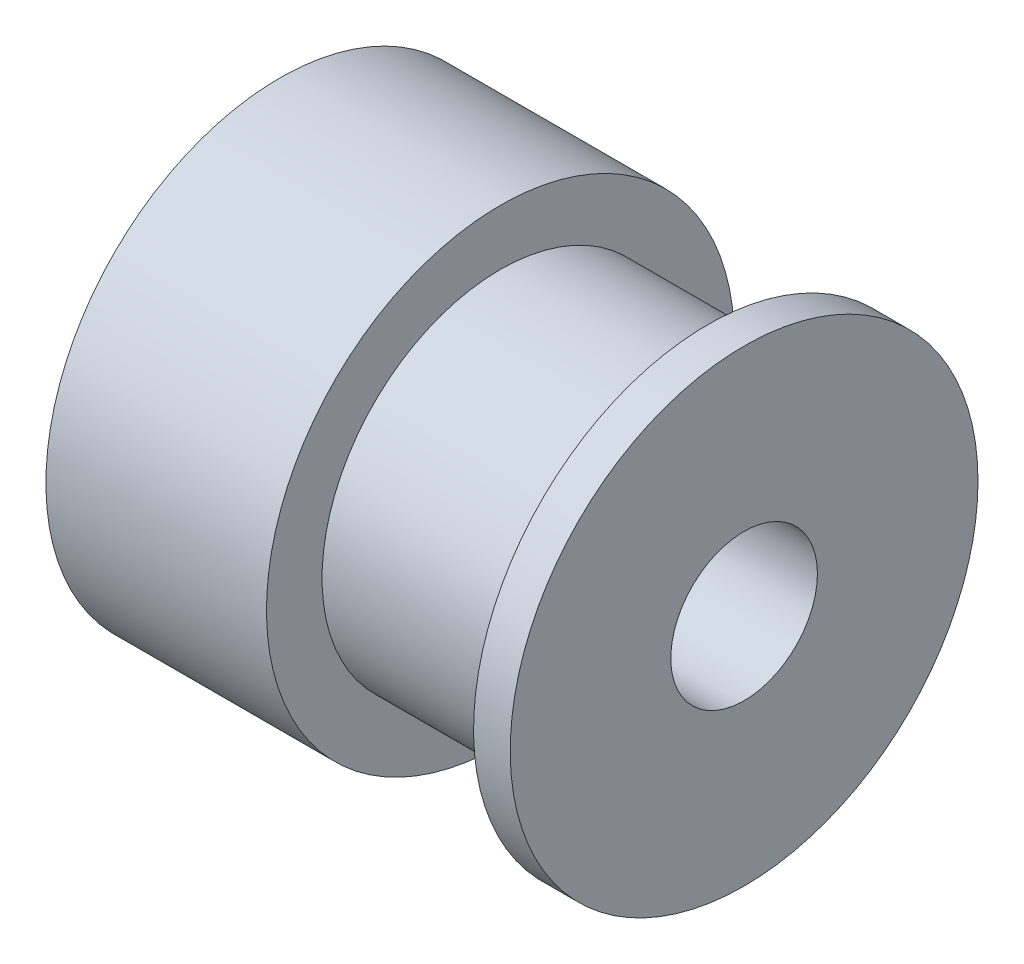
SolidWorks part; units mm, degrees
ref_plane "Front Plane" through (0, 0, 0) normal (0, 0, 1) x (1, 0, 0)
ref_plane "Top Plane" through (0, 0, 0) normal (0, 1, 0) x (1, 0, 0)
ref_plane "Right Plane" through (0, 0, 0) normal (1, 0, 0) x (0, 0, -1)
sketch "Sketch1" plane through (0, 0, 0) normal (1, 0, 0) x (0, 0, -1)
  circle A0 centre (0, 0) radius 7.975
  dimension "D1" = 15.95
extrude "Boss-Extrude1" add sketch "Sketch1" along normal blind 15.83
sketch "Sketch2" plane through (0, 0, 0) normal (0, 0, 1) x (1, 0, 0)
  line L0 (0, 0) -> (7.52, 0) construction
  line L1 (15.83, 0) -> (14.58, 0) construction
  line L2 (15.83, -7.975) -> (15.83, 7.975) construction
  line L3 (7.52, 6.08) -> (7.52, -6.08) construction
  line L4 (15.83, 7.975) -> (0, 7.975) construction
  line L5 (7.52, 7.975) -> (14.58, 7.975)
  line L6 (7.52, 7.975) -> (7.52, 6.08)
  line L7 (7.52, 6.08) -> (14.58, 6.08)
  line L8 (14.58, 7.975) -> (14.58, 6.08)
  line L9 (14.58, 6.08) -> (14.58, 0) construction
  point P9 (7.52, 0)
  dimension "D1" = 7.52
  dimension "D2" = 1.25
  dimension "D3" = 12.16
revolve "Cut-Revolve1" cut sketch "Sketch2" angle 360 about L0
sketch "Sketch3" plane through (15.83, 0, 0) normal (1, 0, 0) x (0, 0, -1)
  circle A0 centre (0, 0) radius 2.5
  dimension "D1" = 5
extrude "Cut-Extrude1" cut sketch "Sketch3" against normal through all
